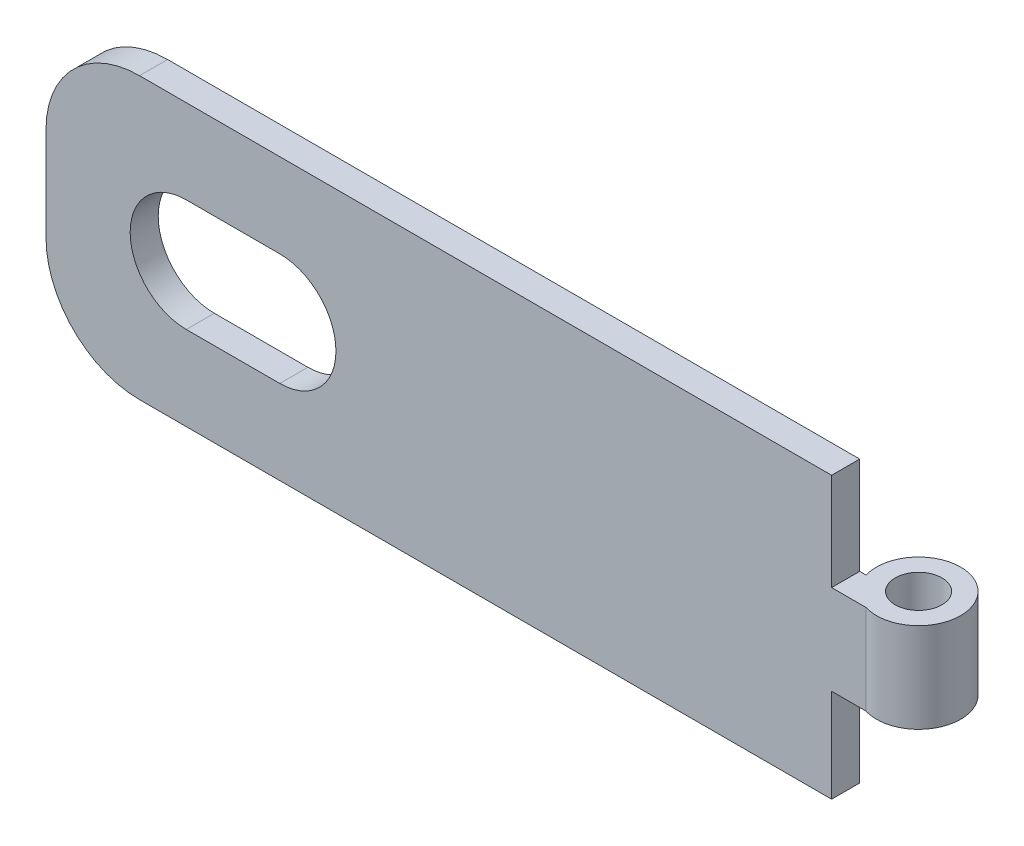
SolidWorks part; units mm, degrees
ref_plane "Спереди" through (0, 0, 0) normal (0, 0, 1) x (1, 0, 0)
ref_plane "Сверху" through (0, 0, 0) normal (0, 1, 0) x (1, 0, 0)
ref_plane "Справа" through (0, 0, 0) normal (1, 0, 0) x (0, 0, -1)
sketch "Эскиз1" plane through (0, 0, 0) normal (0, 1, 0) x (1, 0, 0)
  line L0 (0, 0) -> (88, 0)
extrude "Вытянуть-Тонкостенный1" add sketch "Эскиз1" along normal blind 30 thin
sketch "Эскиз2" plane through (0, 0, 0) normal (0, 1, 0) x (1, 0, 0)
  circle A0 centre (89, 1.3) radius 4.5
extrude "Бобышка-Вытянуть1" add sketch "Эскиз2" along normal blind 30
sketch "Эскиз3" plane through (0, 0, 0) normal (0, 1, 0) x (1, 0, 0)
  circle A0 centre (89, 1.3) radius 2.5
extrude "Вырез-Вытянуть1" cut sketch "Эскиз3" along normal through all
sketch "Эскиз4" plane through (0, 0, 0) normal (0, 0, 1) x (1, 0, 0)
  line L1 (95, 30) -> (84, 30)
  line L2 (95, 30) -> (95, 19.6)
  line L3 (95, 19.6) -> (84, 19.6)
  line L4 (84, 30) -> (84, 19.6)
  line L5 (84, 10) -> (95, 10)
  line L6 (84, 10) -> (84, 0)
  line L7 (84, 0) -> (95, 0)
  line L8 (95, 10) -> (95, 0)
  point P4 (0, 0)
  point P5 (0, 0)
  point P6 (0, 0)
  point P7 (0, 0)
  point P8 (0, 0)
  point P13 (0, 0)
  point P14 (0, 0)
  point P15 (0, 0)
extrude "Вырез-Вытянуть2" cut sketch "Эскиз4" against normal through all both and the other way through all
sketch "Эскиз5" plane through (0, 0, 3) normal (0, 0, 1) x (1, 0, 0)
  line L0 (15, 21) -> (25, 21)
  line L1 (15, 9) -> (25, 9)
  line L2 (10, 30) -> (0, 30)
  line L3 (0, 30) -> (84, 30) construction
  line L4 (0, 30) -> (0, 20)
  line L6 (0, 10) -> (0, 0)
  line L7 (0, 30) -> (0, 0) construction
  line L8 (0, 0) -> (10, 0)
  line L9 (0, 0) -> (84, 0) construction
  arc A0 (15, 21) -> (15, 9) centre (15, 15) ccw
  arc A1 (25, 21) -> (25, 9) centre (25, 15) cw
  arc A2 (10, 30) -> (0, 20) centre (10, 20) ccw
  arc A3 (0, 10) -> (10, 0) centre (10, 10) ccw
extrude "Вырез-Вытянуть3" cut sketch "Эскиз5" against normal through all
